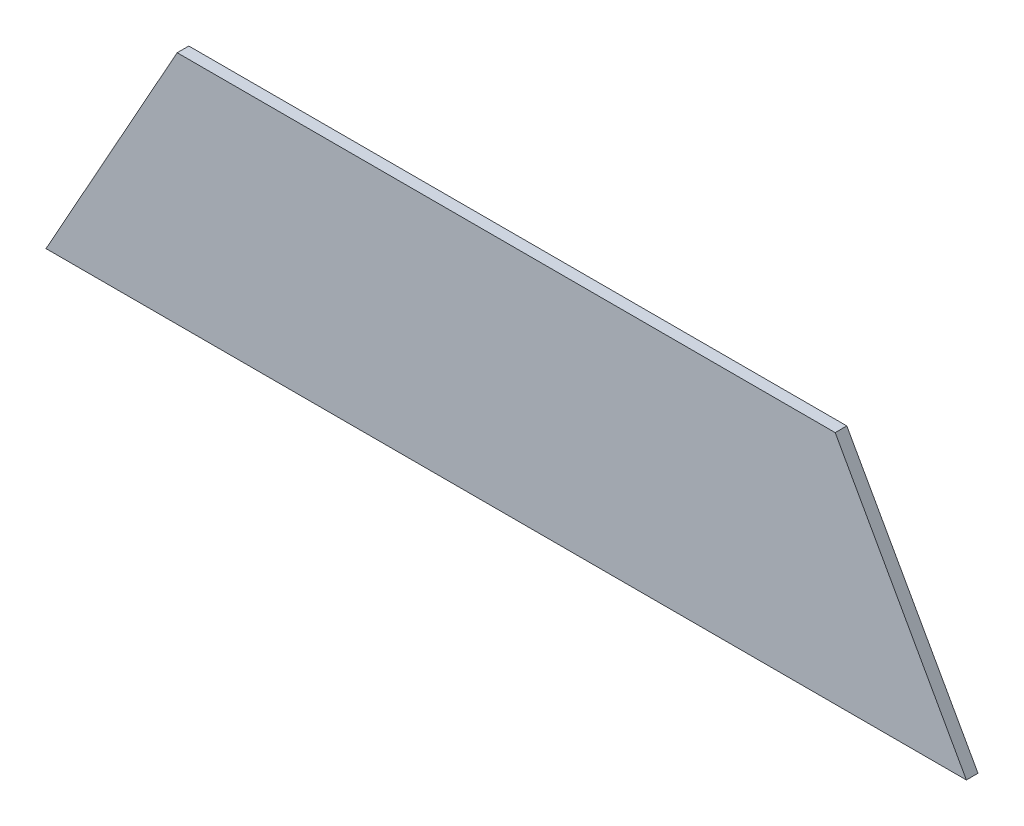
SolidWorks part; units mm, degrees
material "Pine"
ref_plane "Front Plane" through (0, 0, 0) normal (0, 0, 1) x (1, 0, 0)
ref_plane "Top Plane" through (0, 0, 0) normal (0, 1, 0) x (1, 0, 0)
ref_plane "Right Plane" through (0, 0, 0) normal (1, 0, 0) x (0, 0, -1)
sketch "Sketch1" plane through (0, 0, 0) normal (0, 0, 1) x (1, 0, 0)
  line L0 (-471.5503, -687.093) -> (-337.1149, -446.0301)
  line L1 (-337.1149, -446.0301) -> (337.1149, -446.0301)
  line L2 (337.1149, -446.0301) -> (471.5503, -687.093)
  line L3 (471.5503, -687.093) -> (-471.5503, -687.093)
  line L4 (-337.1149, -446.0301) -> (-471.5503, -687.093) construction
  line L5 (337.1149, -446.0301) -> (-337.1149, -446.0301) construction
  line L6 (471.5503, -687.093) -> (337.1149, -446.0301) construction
  line L7 (-471.5503, -687.093) -> (471.5503, -687.093) construction
extrude "Boss-Extrude1" add sketch "Sketch1" against normal up to surface (11.9063 mm away)
